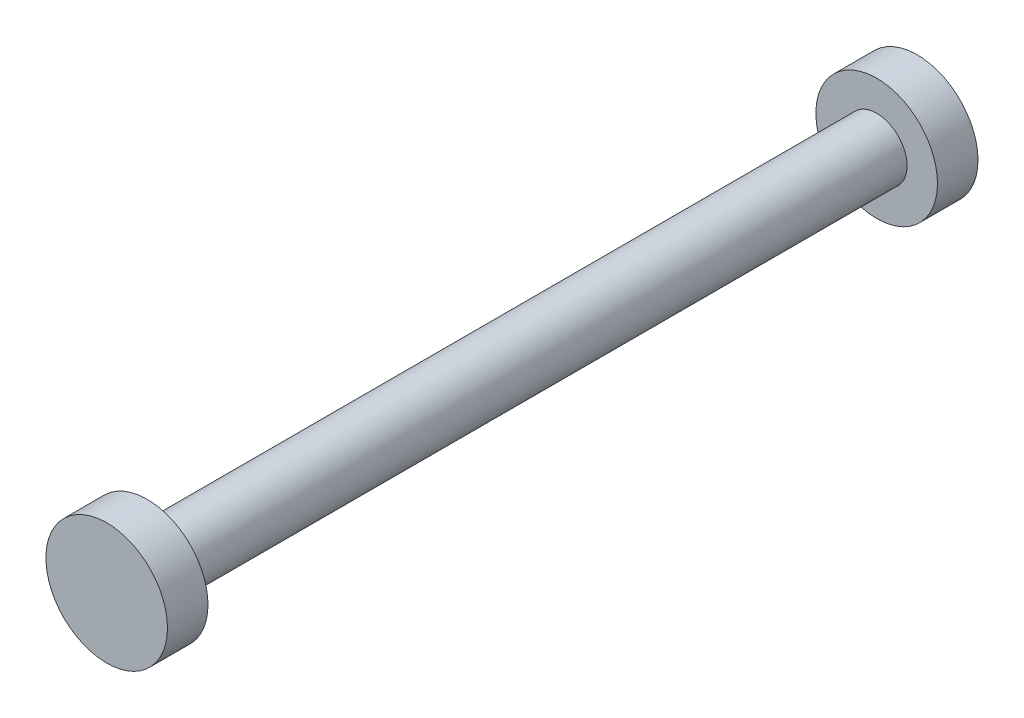
SolidWorks part; units mm, degrees
ref_plane "Front" through (0, 0, 0) normal (0, 0, 1) x (1, 0, 0)
ref_plane "Top" through (0, 0, 0) normal (0, 1, 0) x (1, 0, 0)
ref_plane "Right" through (0, 0, 0) normal (1, 0, 0) x (0, 0, -1)
sketch "Sketch1" plane through (0, 0, 0) normal (0, 0, 1) x (1, 0, 0)
  circle A0 centre (0, 0) radius 1.905
  dimension "D1" = 3.81
extrude "Boss-Extrude1" add sketch "Sketch1" along normal blind 45.72
ref_plane "Plane1" through (0, 0, 22.86) normal (0, 0, 1) x (1, 0, 0)
sketch "Sketch4" plane through (0, 0, 45.72) normal (0, 0, 1) x (1, 0, 0)
  circle A0 centre (0, 0) radius 3.81
  dimension "D1" = 7.62
extrude "Boss-Extrude2" add sketch "Sketch4" along normal blind 2.54
mirror "Mirror1" about plane through (0, 0, 22.86) normal (0, 0, 1) of "Boss-Extrude2"
